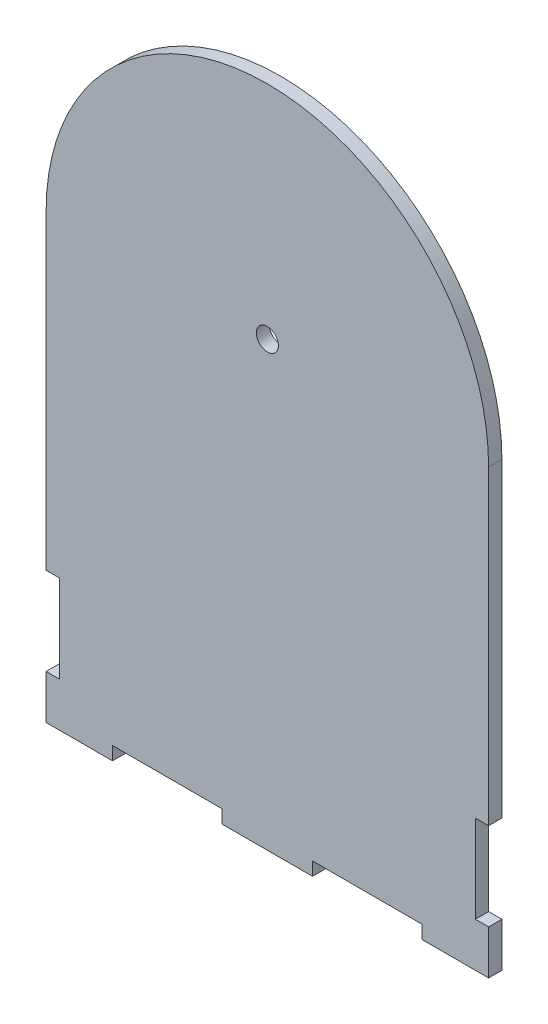
SolidWorks part; units mm, degrees
ref_plane "Front Plane" through (0, 0, 0) normal (0, 0, 1) x (1, 0, 0)
ref_plane "Top Plane" through (0, 0, 0) normal (0, 1, 0) x (1, 0, 0)
ref_plane "Right Plane" through (0, 0, 0) normal (1, 0, 0) x (0, 0, -1)
sketch "Sketch1" plane through (0, 0, 0) normal (0, 0, 1) x (1, 0, 0)
  line L0 (50, -900) -> (50, 49100) construction
  line L1 (0, 0) -> (100, 0)
  line L2 (0, 0) -> (0, 100)
  line L3 (0, 100) -> (100, 100)
  line L4 (100, 0) -> (100, 100)
  line L5 (100, 29.8) -> (97, 29.8)
  line L6 (100, 29.8) -> (100, 10)
  line L7 (100, 10) -> (97, 10)
  line L8 (97, 29.8) -> (97, 10)
  line L9 (0, 10) -> (3, 10)
  line L10 (3, 29.8) -> (3, 10)
  line L11 (0, 29.8) -> (3, 29.8)
  line L12 (0, 29.8) -> (0, 10)
  line L13 (60.2, 0) -> (60.2, 3)
  line L14 (15, 0) -> (39.8, 0)
  line L15 (15, 0) -> (15, 3)
  line L16 (15, 3) -> (39.8, 3)
  line L17 (39.8, 0) -> (39.8, 3)
  line L18 (60.2, 0) -> (85, 0)
  line L19 (85, 0) -> (85, 3)
  line L20 (60.2, 3) -> (85, 3)
  circle A0 centre (50, 100) radius 50
  circle A1 centre (50, 100) radius 2.5
  dimension "D11" = 5
  dimension "D1" = 100
  dimension "D2" = 100
  dimension "D3" = 3
  dimension "D4" = 10
  dimension "D5" = 19.8
  dimension "D6" = 24.8
  dimension "D7" = 3
  dimension "D8" = 15
  dimension "D10" = 15
  dimension "D9" = 2
extrude "Boss-Extrude1" add sketch "Sketch1" along normal blind 3 contours L0 L1 L13 L20 L19 L4 L7 L8 L5 A0 | L1 L0 A0 L2 L11 L10 L9 L15 L16 L17 | L0 A0 L3 A1 | A0 L0 A1 L3 | L0 A1 L3 A0 | A1 L0 A0 L3
